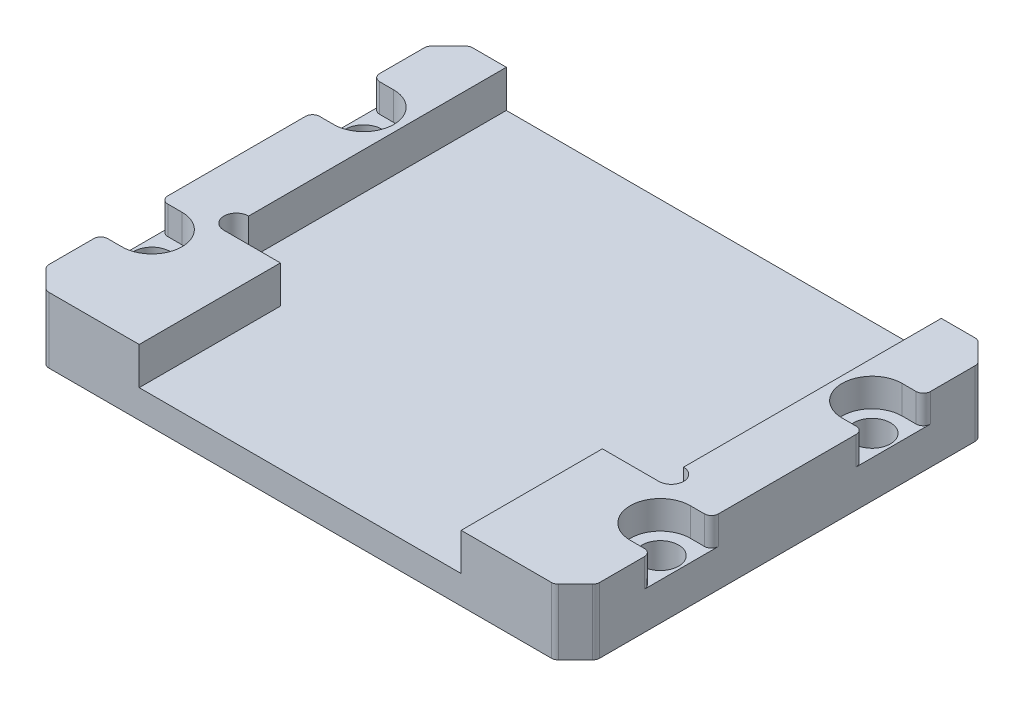
SolidWorks part; units mm, degrees
ref_plane "Front Plane" through (0, 0, 0) normal (0, 0, 1) x (1, 0, 0)
ref_plane "Top Plane" through (0, 0, 0) normal (0, 1, 0) x (1, 0, 0)
ref_plane "Right Plane" through (0, 0, 0) normal (1, 0, 0) x (0, 0, -1)
sketch "Sketch1" plane through (0, 0, 0) normal (0, 1, 0) x (1, 0, 0)
  line L1 (-39, -30) -> (39, -30)
  line L2 (-39, -30) -> (-39, 30)
  line L3 (-39, 30) -> (39, 30)
  line L4 (39, -30) -> (39, 30)
  line L5 (-39, -30) -> (39, 30) construction
  line L6 (-39, 30) -> (39, -30) construction
  point P0 (0, 0)
  dimension "D1" = 78
  dimension "D2" = 60
extrude "Boss-Extrude1" add sketch "Sketch1" along normal blind 9.3
sketch "Sketch2" plane through (0, 9.3, 0) normal (0, 1, 0) x (1, 0, 0)
  line L0 (0, -30) -> (0, 30) construction
  line L1 (39, 30) -> (-39, 30) construction
  line L2 (0, 0) -> (-39, 0) construction
  line L3 (-39, 30) -> (-39, -30) construction
  circle A0 centre (-36, 15) radius 2.5
  circle A1 centre (-36, -15) radius 2.5
  circle A2 centre (36, -15) radius 2.5
  circle A3 centre (36, 15) radius 2.5
  point P6 (0, 0)
  dimension "D3" = 5
  dimension "D1" = 3
  dimension "D2" = 15
hole_wizard "Tap Drill for M5 Tap1" positions "3DSketch1" profile "Sketch3" hole size "M5" standard "GB"
sketch3d "3DSketch1"
  point P0 (-36, 9.3, -15)
  point P3 (-36, 9.3, 15)
  point P6 (36, 9.3, 15)
  point P9 (36, 9.3, -15)
sketch "Sketch3" plane through (-36, 9.3, -15) normal (1, 0, 0) x (0, 0, 1)
  line L0 (0, 0) -> (0, 47.5622)
  line L1 (0, 47.5622) -> (2.6, 46)
  line L2 (2.6, 46) -> (2.6, 0.4)
  line L3 (2.6, 0.4) -> (3, 0)
  line L5 (3, 0) -> (0, 0)
  line L6 (-2.6, 0.4) -> (-3, 0) construction
  line L10 (0, 47.5622) -> (-2.6, 46) construction
  line L11 (0, -6.35) -> (0, 107.95) construction
  dimension "Hole Dia." = 5.2
  dimension "Hole Depth" = 46
  dimension "Near C'Sink Dia." = 6
  dimension "Near C'Sink Angle" = 90
  dimension "Drill Angle" = 118
sketch "Sketch4" plane through (0, 9.3, 0) normal (0, 1, 0) x (1, 0, 0)
  line L0 (-30.8, 30) -> (-30.8, -30)
  line L1 (39, 30) -> (-39, 30) construction
  line L2 (-39, -30) -> (39, -30) construction
  line L3 (-30.8, -30) -> (30.8, -30)
  line L4 (30.8, -30) -> (30.8, 30)
  line L5 (30.8, 30) -> (-30.8, 30)
  line L6 (-39, 15) -> (-39, -15) construction
  line L7 (39, 15) -> (39, 30) construction
  dimension "D1" = 8.2
  dimension "D2" = 8.2
extrude "Cut-Extrude1" cut sketch "Sketch4" against normal offset from surface (5.3 mm away) 4 up to face at (-36, 0, -17.6)
chamfer "Chamfer1" distance 3 angle 45 4 edges at (-39, 4.65, -30) (39, 4.65, -30) (39, 4.65, 30) (-39, 4.65, 30)
sketch "Sketch6" plane through (0, 9.3, 0) normal (0, 1, 0) x (1, 0, 0)
  line L0 (-36, 15) -> (-39.66, 15) construction
  line L1 (-36, 9.821) -> (-36, 20.179) construction
  line L2 (-39.66, 9.4324) -> (-39.66, 20.5676) construction
  line L3 (-39.66, 19.25) -> (-36, 19.25)
  line L4 (-39.66, 10.75) -> (-36, 10.75)
  line L5 (0, 0) -> (-42.8321, 0) construction
  line L6 (0, -30) -> (0, 30) construction
  line L7 (0, 0) -> (0, 30) construction
  line L8 (-39.66, -19.25) -> (-36, -19.25)
  line L9 (-39.66, -10.75) -> (-36, -10.75)
  line L10 (39.66, 19.25) -> (36, 19.25)
  line L11 (39.66, 10.75) -> (36, 10.75)
  line L12 (39.66, -10.75) -> (36, -10.75)
  line L13 (39.66, -19.25) -> (36, -19.25)
  arc A0 (-36, 19.25) -> (-36, 10.75) centre (-36, 15) cw
  arc A1 (-39.66, 10.75) -> (-39.66, 19.25) centre (-39.66, 15) cw
  arc A2 (-39.66, -10.75) -> (-39.66, -19.25) centre (-39.66, -15) ccw
  arc A3 (-36, -19.25) -> (-36, -10.75) centre (-36, -15) ccw
  arc A4 (39.66, 10.75) -> (39.66, 19.25) centre (39.66, 15) ccw
  arc A5 (36, 19.25) -> (36, 10.75) centre (36, 15) ccw
  arc A6 (36, -19.25) -> (36, -10.75) centre (36, -15) cw
  arc A7 (39.66, -10.75) -> (39.66, -19.25) centre (39.66, -15) cw
  point P6 (-36, 15)
  point P11 (-39.66, 15)
  dimension "D1" = 4.25
  dimension "D2" = 4.25
  dimension "D3" = 3.66
extrude "Cut-Extrude2" cut sketch "Sketch6" against normal blind 4
fillet "Fillet1" radius 1 8 edges at (-39, 4.65, -27) (-36, 4.65, -30) (39, 4.65, -27) (36, 4.65, -30) (39, 4.65, 27) (36, 4.65, 30) (-39, 4.65, 27) (-36, 4.65, 30)
fillet "Fillet2" radius 1 8 edges at (-39, 7.3, -19.25) (-39, 7.3, -10.75) (39, 7.3, -10.75) (39, 7.3, -19.25) (39, 7.3, 10.75) (39, 7.3, 19.25) (-39, 7.3, 19.25) (-39, 7.3, 10.75)
sketch "Sketch7" plane through (0, 4, 0) normal (0, 1, 0) x (1, 0, 0)
  line L0 (0, 0) -> (0, -30) construction
  line L1 (-30.8, -30) -> (30.8, -30) construction
  line L2 (-30.8, -30) -> (-30.8, -10)
  line L3 (-30.8, 30) -> (-30.8, -30) construction
  line L4 (-30.8, -10) -> (-22.8, -10)
  line L5 (-22.8, -10) -> (-22.8, -30)
  line L6 (-22.8, -30) -> (-30.8, -30)
  line L7 (22.8, -10) -> (22.8, -30)
  line L8 (30.8, -10) -> (22.8, -10)
  line L9 (30.8, -30) -> (30.8, -10)
  line L10 (22.8, -30) -> (30.8, -30)
  dimension "D1" = 20
  dimension "D2" = 8
extrude "Boss-Extrude2" add sketch "Sketch7" along normal up to surface (5.3 mm away) up to face at (-36.6045, 9.3, 0)
sketch "Sketch8" plane through (0, 9.3, 0) normal (0, 1, 0) x (1, 0, 0)
  line L0 (0, 0) -> (0, -30) construction
  line L1 (-22.8, -30) -> (22.8, -30) construction
  line L2 (30.8, -10) -> (30.8, 30) construction
  circle A0 centre (30.8, -8.25) radius 1.75
  circle A1 centre (-30.8, -8.25) radius 1.75
  dimension "D1" = 3.5
extrude "Cut-Extrude3" cut sketch "Sketch8" against normal up to surface (5.3 mm away) up to face at (0, 4, 5)
